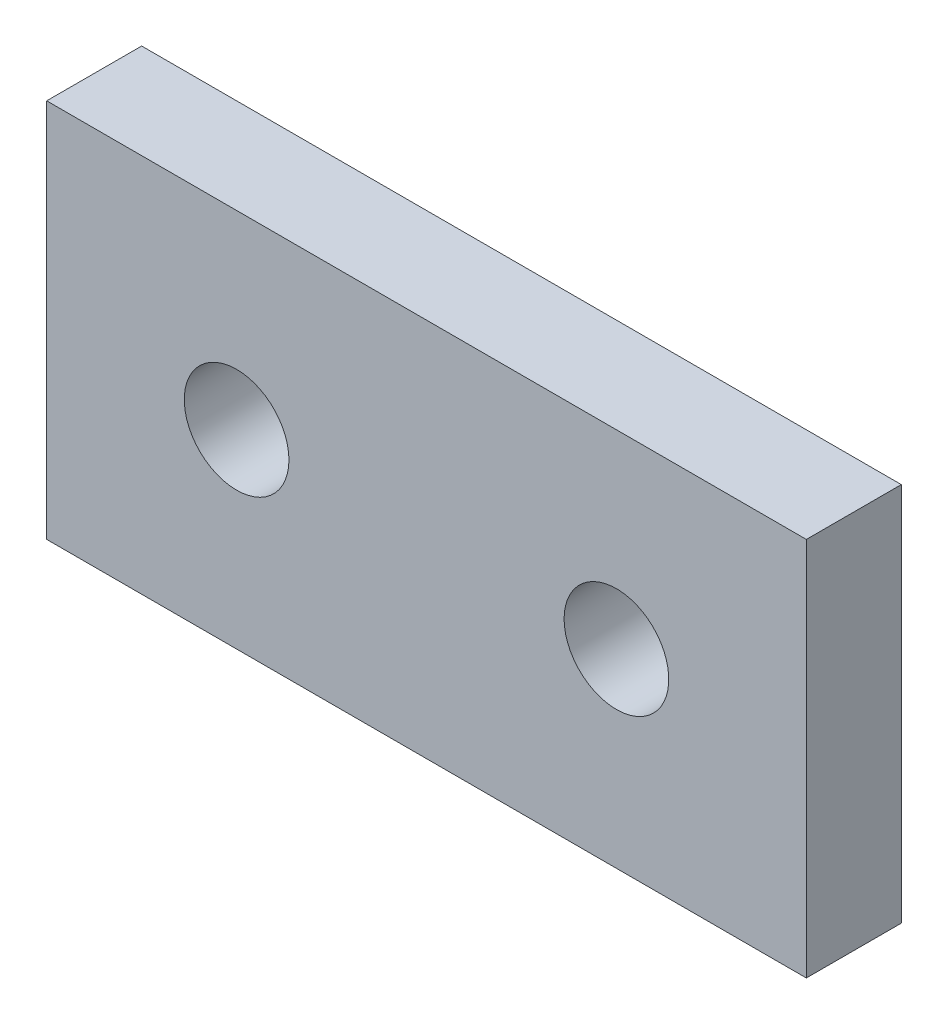
SolidWorks part; units mm, degrees
ref_plane "Front Plane" through (0, 0, 0) normal (0, 0, 1) x (1, 0, 0)
ref_plane "Top Plane" through (0, 0, 0) normal (0, 1, 0) x (1, 0, 0)
ref_plane "Right Plane" through (0, 0, 0) normal (1, 0, 0) x (0, 0, -1)
sketch "Sketch1" plane through (0, 0, 0) normal (0, 0, 1) x (1, 0, 0)
  line L1 (0, 0) -> (50.8, 0)
  line L2 (0, 0) -> (0, 25.4)
  line L3 (0, 25.4) -> (50.8, 25.4)
  line L4 (50.8, 0) -> (50.8, 25.4)
  dimension "D1" = 50.8
  dimension "D2" = 25.4
extrude "Boss-Extrude1" add sketch "Sketch1" along normal blind 6.35
sketch "Sketch2" plane through (0, 0, 6.35) normal (0, 0, 1) x (1, 0, 0)
  line L0 (25.4, 25.4) -> (25.4, 0) construction
  line L1 (50.8, 25.4) -> (0, 25.4) construction
  line L2 (0, 0) -> (50.8, 0) construction
  line L3 (0, 12.7) -> (50.8, 12.7) construction
  line L4 (0, 25.4) -> (0, 0) construction
  line L5 (50.8, 0) -> (50.8, 25.4) construction
  circle A0 centre (12.7, 12.7) radius 3.5
  circle A1 centre (38.1, 12.7) radius 3.5
  dimension "D1" = 7
  dimension "D2" = 12.7
extrude "Cut-Extrude1" cut sketch "Sketch2" against normal blind 6.35
